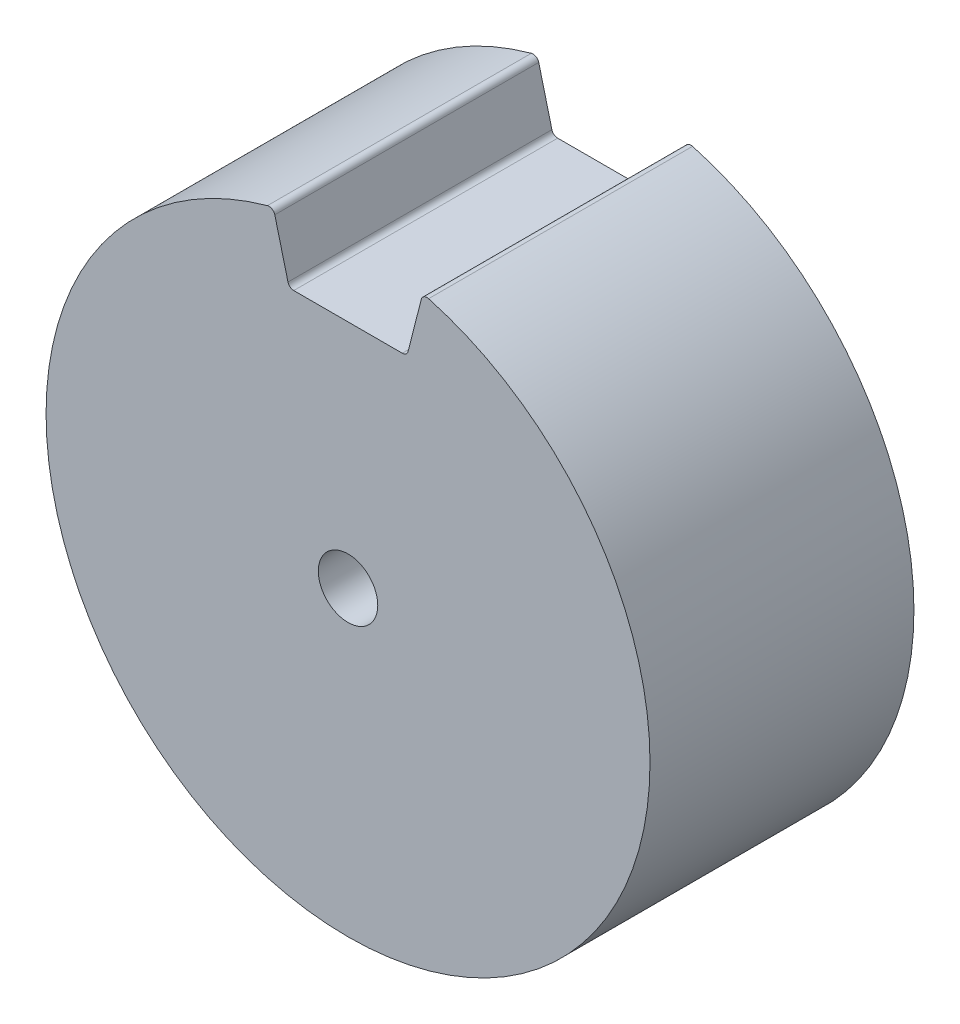
SolidWorks part; units mm, degrees
ref_plane "Front Plane" through (0, 0, 0) normal (0, 0, 1) x (1, 0, 0)
ref_plane "Top Plane" through (0, 0, 0) normal (0, 1, 0) x (1, 0, 0)
ref_plane "Right Plane" through (0, 0, 0) normal (1, 0, 0) x (0, 0, -1)
sketch "Sketch2" plane through (0, 0, 0) normal (0, 0, 1) x (1, 0, 0)
  line L0 (-25.4, 0) -> (25.4, 0) construction
  line L1 (-4.955, 19.4) -> (4.955, 19.4)
  line L2 (-4.955, 19.4) -> (4.955, 19.4) construction
  line L3 (0, 19.4) -> (0, 25.4) construction
  line L4 (4.955, 19.4) -> (6.2857, 24.61)
  line L5 (-4.955, 19.4) -> (-6.2857, 24.61)
  circle A0 centre (0, 0) radius 25.4
  circle A1 centre (0, 0) radius 2.5
  point P4 (0, 0)
  point P10 (0, 19.4)
  dimension "D4" = 5
  dimension "D1" = 50.8
  dimension "D2" = 9.91
  dimension "D3" = 6
extrude "Boss-Extrude2" add sketch "Sketch2" along normal blind 22.2 contours L5 A0 L4 L1 A1
fillet "Fillet1" radius 0.5 4 edges at (4.955, 19.4, 11.1) (6.2857, 24.61, 11.1) (-4.955, 19.4, 11.1) (-6.2857, 24.61, 11.1)
